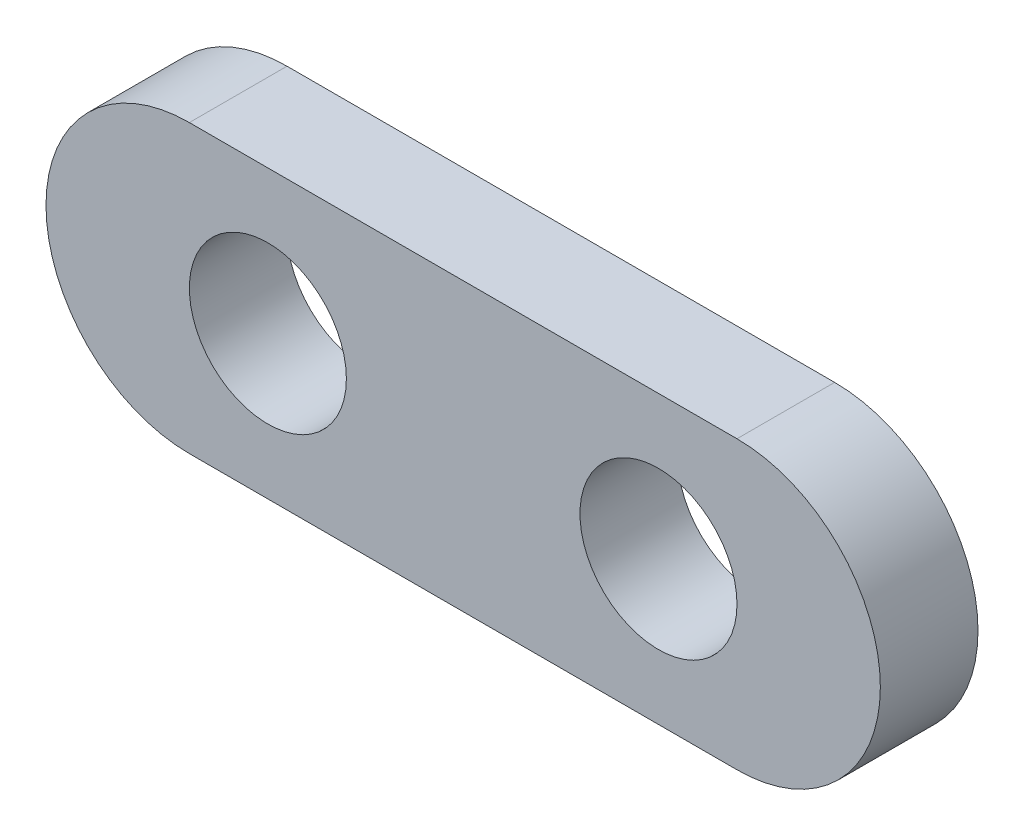
SolidWorks part; units mm, degrees
ref_plane "Спереди" through (0, 0, 0) normal (0, 0, 1) x (1, 0, 0)
ref_plane "Сверху" through (0, 0, 0) normal (0, 1, 0) x (1, 0, 0)
ref_plane "Справа" through (0, 0, 0) normal (1, 0, 0) x (0, 0, -1)
sketch "Эскиз1" plane through (0, 0, 0) normal (0, 0, 1) x (1, 0, 0)
  line L0 (8.9027, 4.6609) -> (-8.9027, 4.6609) construction
  line L1 (8.9027, -4.6609) -> (-8.9027, -4.6609) construction
  line L2 (8.9027, 4.6609) -> (-8.9027, 4.6609)
  line L3 (8.9027, -4.6609) -> (-8.9027, -4.6609)
  arc A0 (8.9027, -4.6609) -> (8.9027, 4.6609) centre (8.9027, 0) ccw construction
  arc A1 (-8.9027, 4.6609) -> (-8.9027, -4.6609) centre (-8.9027, 0) ccw construction
  circle A2 centre (-6.35, 0) radius 2.5527 construction
  circle A3 centre (6.35, 0) radius 2.5527 construction
  arc A4 (8.9027, -4.6609) -> (8.9027, 4.6609) centre (8.9027, 0) ccw
  arc A5 (-8.9027, 4.6609) -> (-8.9027, -4.6609) centre (-8.9027, 0) ccw
  circle A6 centre (-6.35, 0) radius 2.5527
  circle A7 centre (6.35, 0) radius 2.5527
extrude "Бобышка-Вытянуть1" add sketch "Эскиз1" along normal blind 3.175
